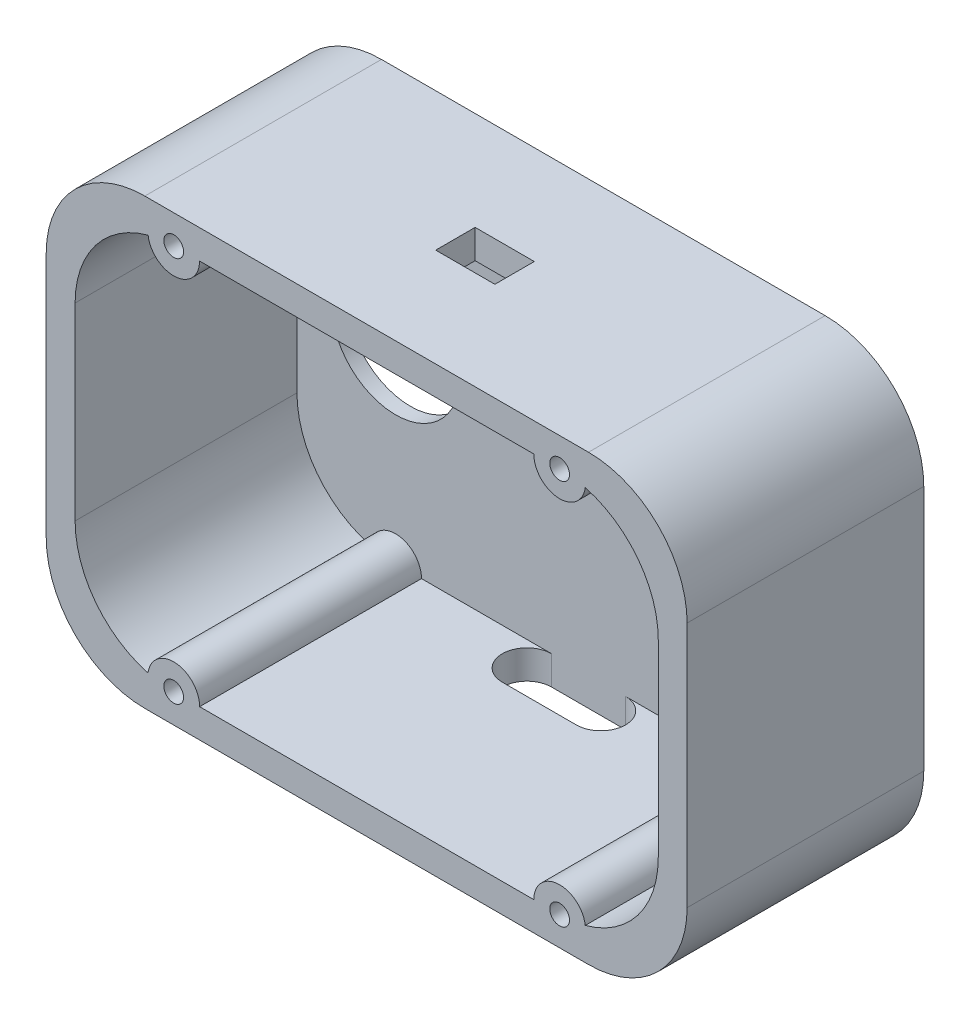
SolidWorks part; units mm, degrees
ref_plane "Front Plane" through (0, 0, 0) normal (0, 0, 1) x (1, 0, 0)
ref_plane "Top Plane" through (0, 0, 0) normal (0, 1, 0) x (1, 0, 0)
ref_plane "Right Plane" through (0, 0, 0) normal (1, 0, 0) x (0, 0, -1)
sketch "Sketch1" plane through (0, 0, 0) normal (0, 0, 1) x (1, 0, 0)
  line L1 (0, 0) -> (130, 0)
  line L2 (0, 0) -> (0, 90)
  line L3 (0, 90) -> (130, 90)
  line L4 (130, 0) -> (130, 90)
  dimension "D1" = 90
  dimension "D2" = 130
extrude "Boss-Extrude1" add sketch "Sketch1" along normal blind 48
fillet "Fillet1" radius 20 4 edges at (0, 90, 24) (0, 0, 24) (130, 0, 24) (130, 90, 24)
sketch "Sketch2" plane through (0, 0, 48) normal (0, 0, 1) x (1, 0, 0)
  line L0 (65, 90) -> (65, 0) construction
  line L1 (110, 90) -> (20, 90) construction
  line L2 (20, 0) -> (110, 0) construction
  line L3 (0, 45) -> (130, 45) construction
  line L4 (0, 70) -> (0, 20) construction
  line L5 (130, 20) -> (130, 70) construction
  line L7 (104.1421, 5.8579) -> (25.8579, 5.8579)
  line L8 (124.1421, 25.8579) -> (124.1421, 64.1421)
  line L9 (104.1421, 84.1421) -> (25.8579, 84.1421)
  line L10 (5.8579, 25.8579) -> (5.8579, 64.1421)
  line L11 (124.1421, 5.8579) -> (5.8579, 84.1421) construction
  line L12 (124.1421, 84.1421) -> (5.8579, 5.8579) construction
  arc A0 (20, 90) -> (0, 70) centre (20, 70) ccw construction
  arc A1 (5.8579, 25.8579) -> (25.8579, 5.8579) centre (25.8579, 25.8579) ccw
  arc A2 (5.8579, 64.1421) -> (25.8579, 84.1421) centre (25.8579, 64.1421) cw
  arc A3 (104.1421, 84.1421) -> (124.1421, 64.1421) centre (104.1421, 64.1421) cw
  arc A4 (124.1421, 25.8579) -> (104.1421, 5.8579) centre (104.1421, 25.8579) cw
  point P12 (65, 45)
  dimension "D1" = 20
extrude "Cut-Extrude4" cut sketch "Sketch2" against normal blind 45
sketch "Sketch3" plane through (0, 0, 3) normal (0, 0, 1) x (1, 0, 0)
  line L0 (25.8579, 5.8579) -> (104.1421, 5.8579) construction
  circle A0 centre (25.8579, 84.1421) radius 5.2407
  circle A1 centre (104.1421, 84.1421) radius 5.2407
  circle A2 centre (25.8579, 5.8579) radius 5.2584
  circle A3 centre (104.1421, 5.8579) radius 5.2407
  arc A4 (104.1421, 5.8579) -> (124.1421, 25.8579) centre (104.1421, 25.8579) ccw construction
  dimension "D1" = 10.4815
  dimension "D2" = 10.4815
  dimension "D3" = 10.5168
  dimension "D4" = 10.4815
extrude "Boss-Extrude2" add sketch "Sketch3" along normal up to surface (45 mm away) up to face at (65, 45, 48)
sketch "Sketch4" plane through (0, 90, 0) normal (0, 1, 0) x (1, 0, 0)
  line L0 (65, 0) -> (65, -48) construction
  line L1 (59, -20) -> (71, -20)
  line L2 (59, -20) -> (59, -28)
  line L3 (59, -28) -> (71, -28)
  line L4 (71, -20) -> (71, -28)
  line L5 (59, -20) -> (71, -28) construction
  line L6 (59, -28) -> (71, -20) construction
  line L7 (110, 0) -> (20, 0) construction
  line L8 (110, -48) -> (20, -48) construction
  line L9 (110, -24) -> (20, -24) construction
  line L10 (110, -48) -> (110, 0) construction
  line L11 (20, 0) -> (20, -48) construction
  point P0 (65, -24)
  point P11 (71, -24)
  dimension "D1" = 8
  dimension "D2" = 12
extrude "Cut-Extrude5" cut sketch "Sketch4" against normal up to next
sketch "Sketch5" plane through (0, 0, 48) normal (0, 0, 1) x (1, 0, 0)
  circle A0 centre (25.8579, 84.1421) radius 2
  circle A1 centre (104.1421, 84.1421) radius 2
  circle A2 centre (104.1421, 5.8579) radius 2
  circle A3 centre (25.8579, 5.8579) radius 2
  dimension "D1" = 4
  dimension "D2" = 4
  dimension "D3" = 4
  dimension "D4" = 4
extrude "Cut-Extrude6" cut sketch "Sketch5" against normal blind 23
sketch "Sketch6" plane through (0, 0, 3) normal (0, 0, 1) x (1, 0, 0)
  line L0 (98.9014, 84.1421) -> (98.9014, 5.8579) construction
  line L1 (124.1421, 45) -> (5.8579, 45) construction
  line L3 (93.4014, 51.4807) -> (93.4014, 38.5193)
  line L5 (104.4014, 51.4807) -> (104.4014, 38.5193)
  line L6 (124.1421, 25.8579) -> (124.1421, 64.1421) construction
  line L7 (5.8579, 64.1421) -> (5.8579, 25.8579) construction
  arc A0 (104.4014, 51.4807) -> (93.4014, 51.4807) centre (98.9014, 45) ccw
  arc A1 (109.3377, 6.5445) -> (98.9014, 5.8579) centre (104.1421, 5.8579) ccw construction
  arc A2 (93.4014, 38.5193) -> (104.4014, 38.5193) centre (98.9014, 45) ccw
  point P17 (104.4014, 45)
  dimension "D1" = 17
  dimension "D2" = 11
  dimension "D3" = 12.9615
extrude "Cut-Extrude7" cut sketch "Sketch6" against normal blind 10
sketch "Sketch7" plane through (0, 0, 3) normal (0, 0, 1) x (1, 0, 0)
  line L0 (124.1421, 45) -> (5.8579, 45) construction
  line L1 (124.1421, 25.8579) -> (124.1421, 64.1421) construction
  line L2 (5.8579, 64.1421) -> (5.8579, 25.8579) construction
  line L3 (25.8579, 84.1421) -> (25.8579, 5.8579) construction
  circle A0 centre (25.8579, 45) radius 13
  dimension "D1" = 26
extrude "Cut-Extrude8" cut sketch "Sketch7" against normal blind 10
sketch "Sketch8" plane through (0, 0, 0) normal (0, 0, -1) x (-1, 0, 0)
  line L0 (-98.9014, 53.5) -> (-98.9014, 90) construction
  line L1 (-110, 90) -> (-20, 90) construction
  line L2 (0, 70) -> (-130, 70) construction
  line L3 (-114.4014, 70) -> (-104.4014, 70)
  line L4 (-114.4014, 70) -> (-114.4014, 60)
  line L5 (-114.4014, 60) -> (-104.4014, 60)
  line L6 (-104.4014, 70) -> (-104.4014, 60)
  line L7 (-114.4014, 70) -> (-104.4014, 60) construction
  line L8 (-114.4014, 60) -> (-104.4014, 70) construction
  line L9 (-93.4014, 70) -> (-83.4014, 70)
  line L10 (-93.4014, 70) -> (-93.4014, 60)
  line L11 (-93.4014, 60) -> (-83.4014, 60)
  line L12 (-83.4014, 70) -> (-83.4014, 60)
  line L13 (-93.4014, 70) -> (-83.4014, 60) construction
  line L14 (-93.4014, 60) -> (-83.4014, 70) construction
  line L15 (-93.4014, 51.4807) -> (-93.4014, 90) construction
  line L16 (-93.4014, 38.5193) -> (-93.4014, 51.4807) construction
  line L17 (-104.4014, 51.4807) -> (-104.4014, 90) construction
  arc A0 (-93.4014, 51.4807) -> (-104.4014, 51.4807) centre (-98.9014, 45) ccw construction
  point P7 (-109.4014, 65)
  point P12 (-88.4014, 65)
  dimension "D1" = 10
  dimension "D2" = 10
  dimension "D3" = 10
  dimension "D4" = 10
extrude "Cut-Extrude9" cut sketch "Sketch8" against normal blind 30
sketch "Sketch9" plane through (0, 0, 0) normal (0, 0, -1) x (-1, 0, 0)
  line L0 (-98.9014, 36.5) -> (-98.9014, 0) construction
  line L1 (-20, 0) -> (-110, 0) construction
  line L2 (-130, 20) -> (0, 20) construction
  line L3 (-93.9014, 20) -> (-103.9014, 20)
  line L4 (-93.9014, 20) -> (-93.9014, 30)
  line L5 (-93.9014, 30) -> (-103.9014, 30)
  line L6 (-103.9014, 20) -> (-103.9014, 30)
  line L7 (-93.9014, 20) -> (-103.9014, 30) construction
  line L8 (-93.9014, 30) -> (-103.9014, 20) construction
  arc A0 (-104.4014, 38.5193) -> (-93.4014, 38.5193) centre (-98.9014, 45) ccw construction
  point P7 (-98.9014, 25)
  dimension "D1" = 10
  dimension "D2" = 10
extrude "Cut-Extrude10" cut sketch "Sketch9" against normal blind 10
sketch "Sketch11" plane through (0, 5.8579, 0) normal (0, 1, 0) x (1, 0, 0)
  line L0 (57.5088, -8) -> (72.5088, -8) construction
  line L1 (57.5088, -3) -> (72.5088, -3)
  line L2 (57.5088, -13) -> (72.5088, -13)
  line L3 (31.1163, -3) -> (93.4265, -3) construction
  line L4 (31.1163, -3) -> (98.9014, -3) construction
  line L5 (31.1163, -48) -> (31.1163, -3) construction
  line L6 (65.0088, -48) -> (65.0088, -3) construction
  line L7 (31.1163, -48) -> (98.9014, -48) construction
  arc A0 (57.5088, -3) -> (57.5088, -13) centre (57.5088, -8) ccw
  arc A1 (72.5088, -13) -> (72.5088, -3) centre (72.5088, -8) ccw
  point P2 (65.0088, -8)
  dimension "D1" = 5
  dimension "D2" = 15
extrude "Cut-Extrude11" cut sketch "Sketch11" against normal blind 10 contours A1 L1 A0 L2
